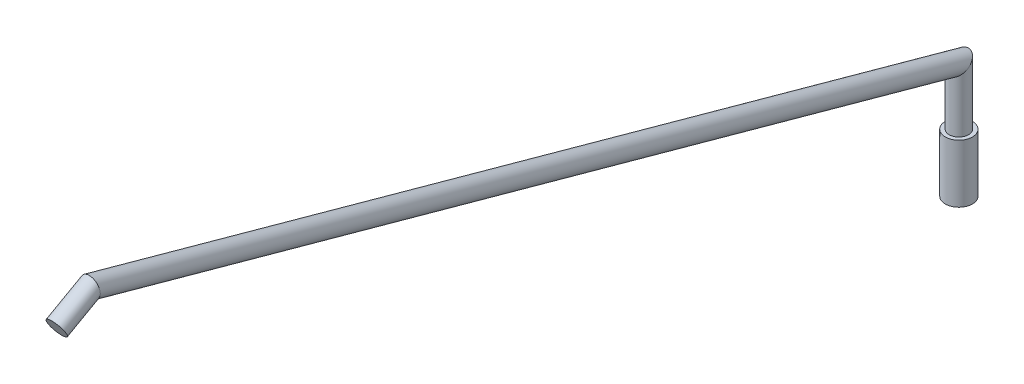
SolidWorks part; units mm, degrees
ref_plane "Front Plane" through (0, 0, 0) normal (0, 0, 1) x (1, 0, 0)
ref_plane "Top Plane" through (0, 0, 0) normal (0, 1, 0) x (1, 0, 0)
ref_plane "Right Plane" through (0, 0, 0) normal (1, 0, 0) x (0, 0, -1)
sketch "Sketch1" plane through (0, 0, 0) normal (1, 0, 0) x (0, 0, -1)
  line L0 (0, 0) -> (0, 30)
  line L1 (0, 30) -> (-224.2774, 91.8904)
  line L2 (-224.2774, 91.8904) -> (-233, 87)
  dimension "D1" = 233
  dimension "D2" = 87
  dimension "D3" = 30
  dimension "D4" = 10
ref_plane "Plane1" through (0, 87, 233) normal (0, -0.489, 0.8723) x (1, 0, 0)
sketch "Sketch2" plane through (0, 87, 233) normal (0, -0.489, 0.8723) x (1, 0, 0)
  circle A2 centre (0, 0) radius 2.5
  dimension "D1" = 5
sweep "Sweep1" add profiles "Sketch2" path "Sketch1"
sketch "Sketch3" plane through (0, 0, 0) normal (0, -1, 0) x (1, 0, 0)
  circle A2 centre (0, 0) radius 3.5
  circle A3 centre (0, 0) radius 3.5
  dimension "D1" = 1
extrude "Boss-Extrude1" add sketch "Sketch3" against normal blind 15
ref_plane "Attach to Counter Plane" through (0, 0, 0) normal (0, -1, 0) x (-1, 0, 0)
